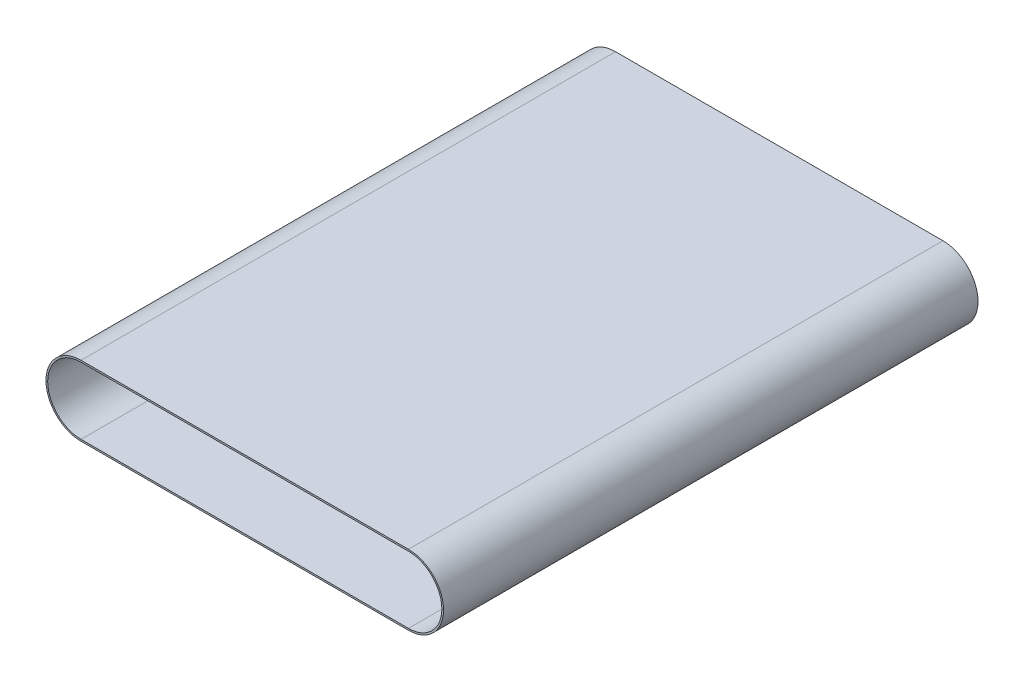
SolidWorks part; units mm, degrees
ref_plane "Alzado" through (0, 0, 0) normal (0, 0, 1) x (1, 0, 0)
ref_plane "Planta" through (0, 0, 0) normal (0, 1, 0) x (1, 0, 0)
ref_plane "Vista lateral" through (0, 0, 0) normal (1, 0, 0) x (0, 0, -1)
sketch "Croquis1" plane through (0, 0, 0) normal (0, 0, 1) x (1, 0, 0)
  line L0 (-122.5, 0) -> (122.5, 0) construction
  line L1 (-122.5, 25) -> (122.5, 25)
  line L2 (-122.5, -25) -> (122.5, -25)
  line L3 (-122.5, 26.25) -> (122.5, 26.25)
  line L4 (122.5, -26.25) -> (-122.5, -26.25)
  arc A0 (-122.5, 25) -> (-122.5, -25) centre (-122.5, 0) ccw
  arc A1 (-122.5, 26.25) -> (-122.5, -26.25) centre (-122.5, 0) ccw
  arc A2 (122.5, -25) -> (122.5, 25) centre (122.5, 0) ccw
  arc A3 (122.5, -26.25) -> (122.5, 26.25) centre (122.5, 0) ccw
  point P4 (0, 0)
  dimension "D1" = 245
  dimension "D2" = 52.5
  dimension "D3" = 50
extrude "Saliente-Extruir2" add sketch "Croquis1" along normal blind 400
